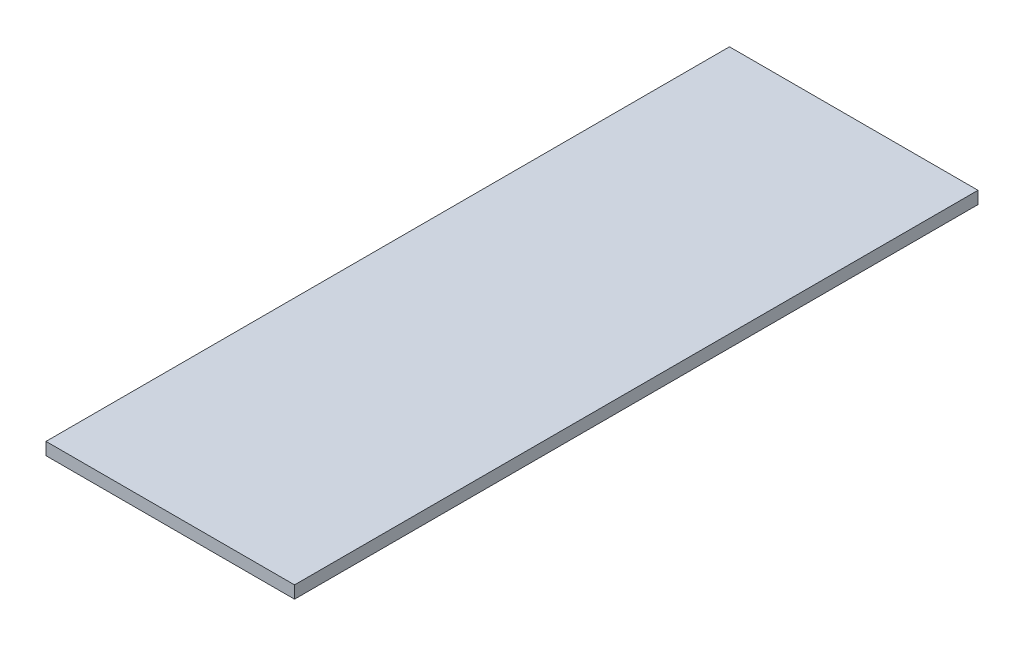
SolidWorks part; units mm, degrees
ref_plane "Front Plane" through (0, 0, 0) normal (0, 0, 1) x (1, 0, 0)
ref_plane "Top Plane" through (0, 0, 0) normal (0, 1, 0) x (1, 0, 0)
ref_plane "Right Plane" through (0, 0, 0) normal (1, 0, 0) x (0, 0, -1)
sketch "Sketch1" plane through (0, 0, 0) normal (0, 1, 0) x (1, 0, 0)
  line L1 (-12.7, -34.925) -> (12.7, -34.925)
  line L2 (-12.7, -34.925) -> (-12.7, 34.925)
  line L3 (-12.7, 34.925) -> (12.7, 34.925)
  line L4 (12.7, -34.925) -> (12.7, 34.925)
  line L5 (-12.7, -34.925) -> (12.7, 34.925) construction
  line L6 (-12.7, 34.925) -> (12.7, -34.925) construction
  point P0 (0, 0)
  dimension "D1" = 69.85
  dimension "D2" = 25.4
extrude "Boss-Extrude1" add sketch "Sketch1" along normal blind 1.27
